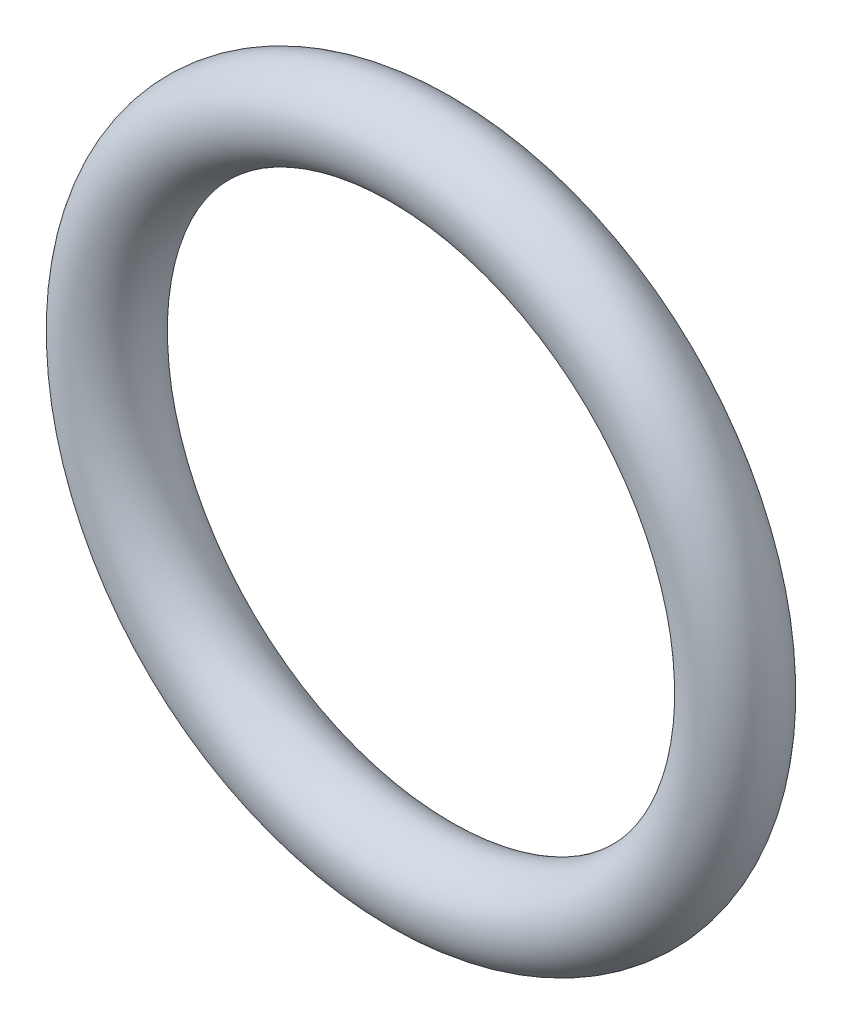
SolidWorks part; units mm, degrees
ref_plane "Front Plane" through (0, 0, 0) normal (0, 0, 1) x (1, 0, 0)
ref_plane "Top Plane" through (0, 0, 0) normal (0, 1, 0) x (1, 0, 0)
ref_plane "Right Plane" through (0, 0, 0) normal (1, 0, 0) x (0, 0, -1)
sketch "Sketch1" plane through (0, 0, 0) normal (0, 0, 1) x (1, 0, 0)
  circle A0 centre (0, 0) radius 17.4625
  dimension "D1" = 34.925
sketch "Sketch2" plane through (0, 0, 0) normal (1, 0, 0) x (0, 0, -1)
  line L0 (0, 17.4625) -> (0, -17.4625) construction
  line L1 (0, 17.4625) -> (0, -17.4625)
  circle A0 centre (0, 17.4625) radius 2.3813
  dimension "D1" = 4.7625
sweep "Sweep1" add profiles "Sketch2" path "Sketch1"
